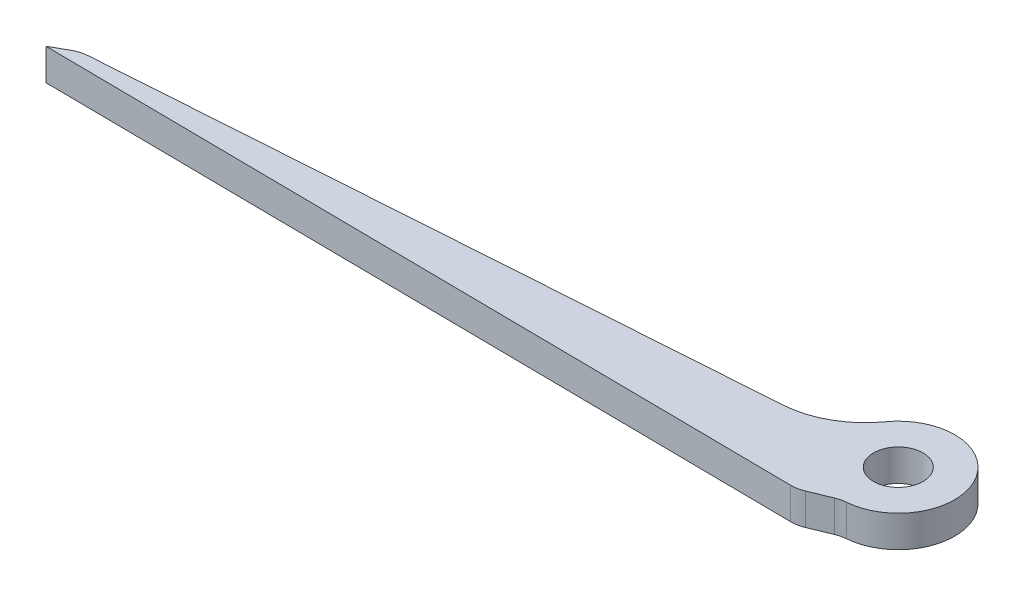
SolidWorks part; units mm, degrees
material "AISI Type A2 Tool Steel"
ref_plane "Front Plane" through (0, 0, 0) normal (0, 0, 1) x (1, 0, 0)
ref_plane "Top Plane" through (0, 0, 0) normal (0, 1, 0) x (1, 0, 0)
ref_plane "Right Plane" through (0, 0, 0) normal (1, 0, 0) x (0, 0, -1)
other "Bounding Box"
ref_plane "Default Plane" through (-8.9266, -12.7485, 0) normal (-0.1736, 0.9848, 0) x (0.9848, 0.1736, 0)
sketch "Sketch1" plane through (0, 0, 0) normal (0, 1, 0) x (1, 0, 0)
  line L0 (-5.6642, 0) -> (-77.1792, -4.9356)
  line L1 (-77.1792, -4.9356) -> (-79.392, -6.1825)
  line L2 (-79.392, -6.1825) -> (-3.192, -6.9784)
  line L3 (-3.192, -6.9784) -> (0, -5.6642)
  circle A0 centre (0, 0) radius 2.4892
  arc A1 (0, -5.6642) -> (-5.6642, 0) centre (0, 0) ccw
  dimension "D1" = 4.9784
  dimension "D2" = 3.175
  dimension "D3" = 76.2
  dimension "D4" = 2.54
  dimension "D5" = 30
  dimension "D6" = 71.6851
  dimension "D7" = 154.546
  dimension "D8" = 7.132
extrude "Boss-Extrude1" add sketch "Sketch1" along normal blind 3.175
fillet "Fillet1" radius 3.175 3 edges at (-77.1792, 1.5875, 4.9356) (-3.192, 1.5875, 6.9784) (0, 1.5875, 5.6642)
fillet "Fillet2" radius 8.89 1 edges at (-5.6642, 1.5875, 0)
